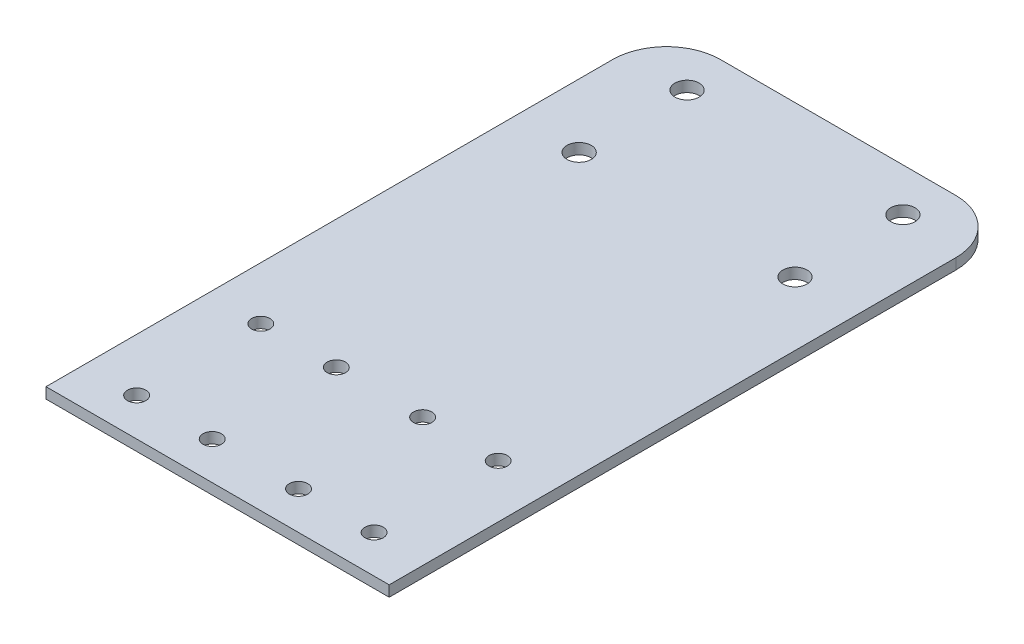
SolidWorks part; units mm, degrees
material "6061 Alloy"
ref_plane "Front Plane" through (0, 0, 0) normal (0, 0, 1) x (1, 0, 0)
ref_plane "Top Plane" through (0, 0, 0) normal (0, 1, 0) x (1, 0, 0)
ref_plane "Right Plane" through (0, 0, 0) normal (1, 0, 0) x (0, 0, -1)
sketch "Sketch2" plane through (0, 0, 0) normal (1, 0, 0) x (0, 0, -1)
  line L0 (0, 0) -> (0, 2)
  line L1 (0, 2) -> (-35, 2)
  line L2 (-35, 2) -> (-55, 2)
  line L3 (-55, 2) -> (-115, 2)
  line L4 (0, 0) -> (-35, 0)
  line L5 (-115, 2) -> (-115, 0)
  line L6 (-35, 0) -> (-55, 0)
  line L7 (-55, 0) -> (-115, 0)
  line L8 (-2, 0) -> (-2, 0) construction
  line L9 (-2, 0) -> (-35, 0) construction
  dimension "D2" = 60
  dimension "D3" = 115
  dimension "D5" = 35
  dimension "D1" = 2
extrude "Sheet Extrude" add sketch "Sketch2" along normal mid plane 63.6
hole_wizard "M3 Clearance Hole1" positions "Sketch5" profile "Sketch6" hole size "M3" standard "ANSI Metric"
sketch "Sketch5" plane through (0, 2, 0) normal (0, 1, 0) x (1, 0, 0)
  line L0 (0, -127.4881) -> (0, -27.1774) construction
  line L2 (31.8, -115) -> (-31.8, -115) construction
  point P0 (-22, -108)
  point P2 (-22, -85)
  point P4 (-8, -85)
  point P6 (-8, -108)
  point P16 (22, -108)
  point P17 (8, -108)
  point P18 (8, -85)
  point P19 (22, -85)
  dimension "D1" = 23
  dimension "D2" = 14
  dimension "D3" = 8
  dimension "D4" = 7
sketch "Sketch6" plane through (-22, 2, 108) normal (1, 0, 0) x (0, 0, 1)
  line L0 (0, 0) -> (0, 9.5215)
  line L1 (0, 9.5215) -> (1.7, 8.5)
  line L2 (1.7, 8.5) -> (1.7, 0)
  line L5 (1.7, 0) -> (0, 0)
  line L10 (0, 9.5215) -> (-1.7, 8.5) construction
  line L11 (0, -6.35) -> (0, 107.95) construction
  dimension "Hole Dia." = 3.4
  dimension "Hole Depth" = 8.5
  dimension "Drill Angle" = 118
hole_wizard "M4 Clearance Hole1" positions "Sketch7" profile "Sketch8" hole size "M4" standard "ANSI Metric"
sketch "Sketch7" plane through (0, 2, 0) normal (0, 1, 0) x (1, 0, 0)
  line L0 (0, 6.97) -> (0, -46.1018) construction
  line L2 (-31.8, -18) -> (52.4815, -18) construction
  line L4 (31.8, 0) -> (-31.8, 0) construction
  point P0 (-20, -28)
  point P2 (20, -28)
  point P4 (20, -8)
  point P6 (-20, -8)
  dimension "D1" = 10
  dimension "D2" = 10
  dimension "D3" = 20
  dimension "D4" = 20
  dimension "D5" = 8
sketch "Sketch8" plane through (-20, 2, 28) normal (1, 0, 0) x (0, 0, 1)
  line L0 (0, 0) -> (0, 9.8519)
  line L1 (0, 9.8519) -> (2.25, 8.5)
  line L2 (2.25, 8.5) -> (2.25, 0)
  line L5 (2.25, 0) -> (0, 0)
  line L10 (0, 9.8519) -> (-2.25, 8.5) construction
  line L11 (0, -6.35) -> (0, 107.95) construction
  dimension "Hole Dia." = 4.5
  dimension "Hole Depth" = 8.5
  dimension "Drill Angle" = 118
fillet "Fillet1" radius 10 2 edges at (-31.8, 1, 0) (31.8, 1, 0)
